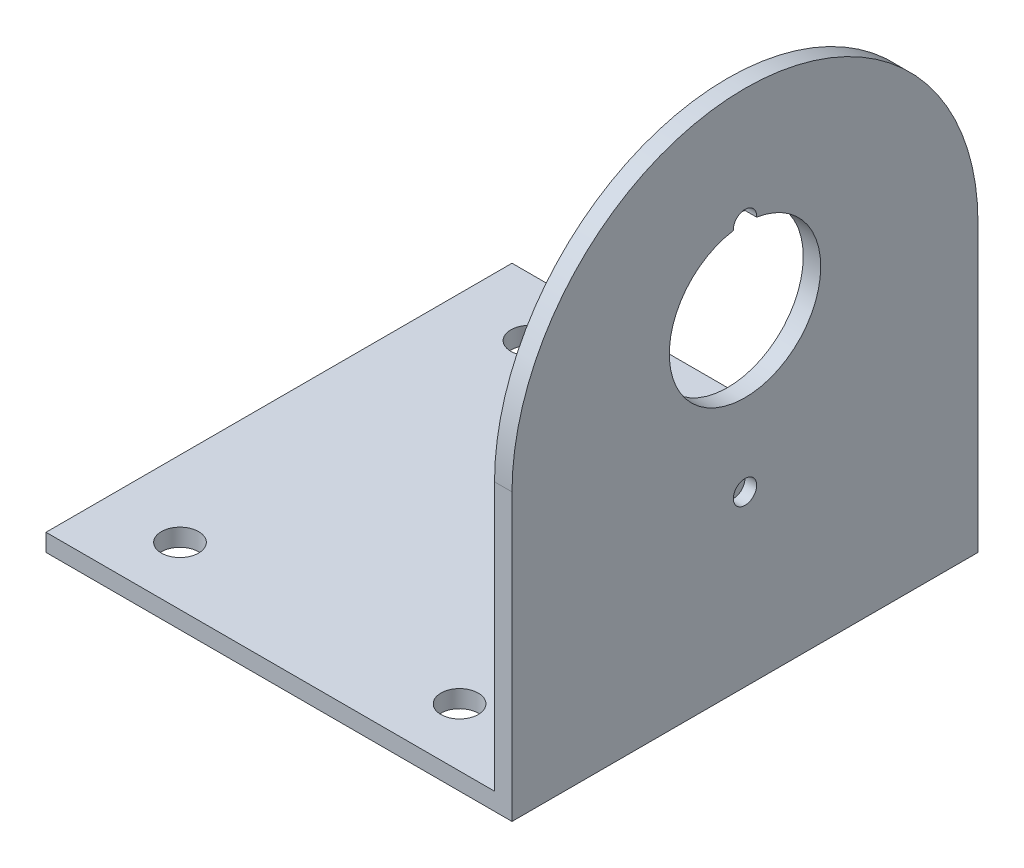
SolidWorks part; units mm, degrees
ref_plane "前视基准面" through (0, 0, 0) normal (0, 0, 1) x (1, 0, 0)
ref_plane "上视基准面" through (0, 0, 0) normal (0, 1, 0) x (1, 0, 0)
ref_plane "右视基准面" through (0, 0, 0) normal (1, 0, 0) x (0, 0, -1)
sketch "草图1" plane through (0, 0, 0) normal (0, 1, 0) x (1, 0, 0)
  line L1 (15, -27.5) -> (-25, -27.5)
  line L2 (15, -27.5) -> (15, 12.5)
  line L3 (15, 12.5) -> (-25, 12.5)
  line L4 (-25, -27.5) -> (-25, 12.5)
  point P0 (0, 0)
  dimension "D1" = 40
  dimension "D2" = 40
extrude "凸台-拉伸1" add sketch "草图1" along normal blind 1.5
sketch "草图3" plane through (15, 0, 0) normal (1, 0, 0) x (0, 0, -1)
  line L0 (-27.5, 1.5) -> (12.5, 1.5)
  line L1 (12.5, 1.5) -> (12.5, 24.5)
  line L3 (-27.5, 24.5) -> (-27.5, 1.5)
  line L4 (-7.5, 44.5) -> (-7.5, 1.5) construction
  line L5 (-27.5, 24.5) -> (12.5, 24.5) construction
  arc A0 (12.5, 24.5) -> (-27.5, 24.5) centre (-7.5, 24.5) ccw
  dimension "D1" = 23
extrude "凸台-拉伸2" add sketch "草图3" against normal blind 1.5
sketch "草图4" plane through (0, 0, 0) normal (0, -1, 0) x (1, 0, 0)
  line L3 (-25, 7.5) -> (15, 7.5) construction
  line L4 (-25, -12.5) -> (-25, 27.5) construction
  line L5 (15, 27.5) -> (15, -12.5) construction
  circle A0 centre (-18.5, 22.5) radius 1.6
  circle A3 centre (-18.5, -7.5) radius 1.6
  circle A4 centre (5.5, 22.5) radius 1.6
  circle A5 centre (5.5, -7.5) radius 1.6
  dimension "D1" = 6.5
  dimension "D3" = 24
  dimension "D2" = 15
extrude "切除-拉伸1" cut sketch "草图4" against normal through all
sketch "草图6" plane through (15, 0, 0) normal (1, 0, 0) x (0, 0, -1)
  line L0 (-7.5, 44.5) -> (-7.5, 0) construction
  line L1 (-27.5, 0) -> (12.5, 0) construction
  arc A0 (12.5, 24.5) -> (-27.5, 24.5) centre (-7.5, 24.5) ccw construction
  circle A1 centre (-7.5, 28) radius 6.5
  dimension "D1" = 28
extrude "切除-拉伸2" cut sketch "草图6" against normal through all
sketch "草图7" plane through (15, 0, 0) normal (1, 0, 0) x (0, 0, -1)
  line L0 (-7.5, 28) -> (-7.5, 0) construction
  line L1 (-27.5, 0) -> (12.5, 0) construction
  line L2 (-27.5, 24.5) -> (12.5, 24.5) construction
  circle A0 centre (-7.5, 14.5) radius 1
  circle A1 centre (-7.5, 34.5) radius 1
  point P11 (-7.5, 24.5)
  dimension "D1" = 10
extrude "切除-拉伸3" cut sketch "草图7" against normal blind 1
